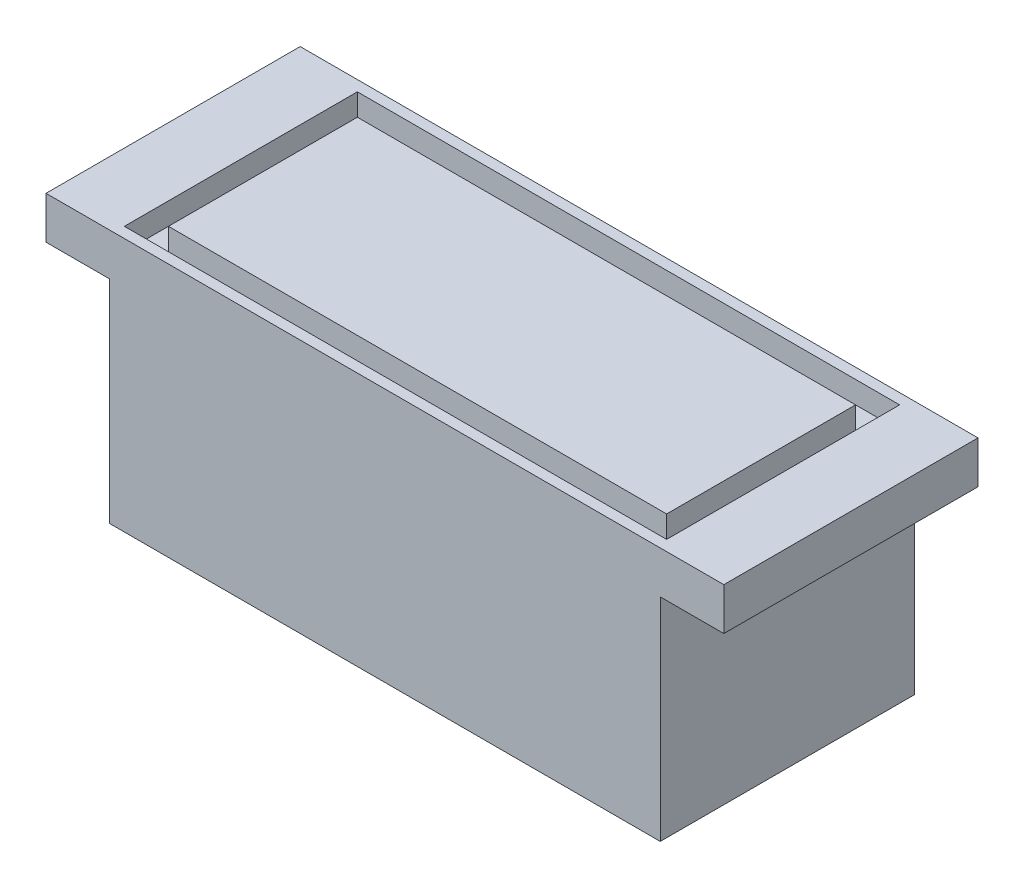
SolidWorks part; units mm, degrees
ref_plane "Front Plane" through (0, 0, 0) normal (0, 0, 1) x (1, 0, 0)
ref_plane "Top Plane" through (0, 0, 0) normal (0, 1, 0) x (1, 0, 0)
ref_plane "Right Plane" through (0, 0, 0) normal (1, 0, 0) x (0, 0, -1)
sketch "Sketch1" plane through (0, 0, 0) normal (0, 0, 1) x (1, 0, 0)
  line L0 (-50.8, 0) -> (-50.8, -6.35)
  line L1 (-50.8, -6.35) -> (-41.275, -6.35)
  line L2 (-41.275, -6.35) -> (-41.275, -38.1)
  line L3 (-41.275, -38.1) -> (41.275, -38.1)
  line L4 (0, -38.1) -> (0, 0)
  line L5 (50.8, 0) -> (-50.8, 0)
  line L6 (41.275, -6.35) -> (41.275, -38.1)
  line L7 (50.8, -6.35) -> (41.275, -6.35)
  line L8 (50.8, 0) -> (50.8, -6.35)
  point P11 (-15.875, -38.1)
  point P12 (-41.275, -38.1)
  point P13 (36.4644, -38.1)
  dimension "D1" = 6.35
  dimension "D2" = 9.525
  dimension "D4" = 50.8
  dimension "D5" = 38.1
extrude "Boss-Extrude1" add sketch "Sketch1" along normal blind 38.1 contours L3 L6 L7 L8 L5 L0 L1 L2
sketch "Sketch2" plane through (0, 0, 0) normal (0, 1, 0) x (1, 0, 0)
  line L0 (-40.64, -1.5875) -> (40.64, -1.5875)
  line L1 (40.64, -1.5875) -> (40.64, -36.5125)
  line L2 (40.64, -36.5125) -> (-40.64, -36.5125)
  line L3 (-40.64, -36.5125) -> (-40.64, -1.5875)
  line L4 (50.8, 0) -> (-50.8, 0) construction
  line L5 (50.8, -38.1) -> (-50.8, -38.1) construction
  line L6 (-50.8, -38.1) -> (-50.8, 0) construction
  line L7 (50.8, -38.1) -> (50.8, 0) construction
  line L8 (-37.338, -4.8895) -> (37.338, -4.8895)
  line L9 (37.338, -4.8895) -> (37.338, -33.2105)
  line L10 (37.338, -33.2105) -> (-37.338, -33.2105)
  line L11 (-37.338, -4.8895) -> (-37.338, -33.2105)
  dimension "D1" = 1.5875
  dimension "D2" = 1.5875
  dimension "D3" = 10.16
  dimension "D4" = 10.16
  dimension "D5" = 3.302
  dimension "D6" = 3.302
  dimension "D7" = 3.302
  dimension "D8" = 3.302
extrude "Cut-Extrude1" cut sketch "Sketch2" against normal blind 3.302 contours L3 L2 L1 L0 L11 L8 L9 L10
